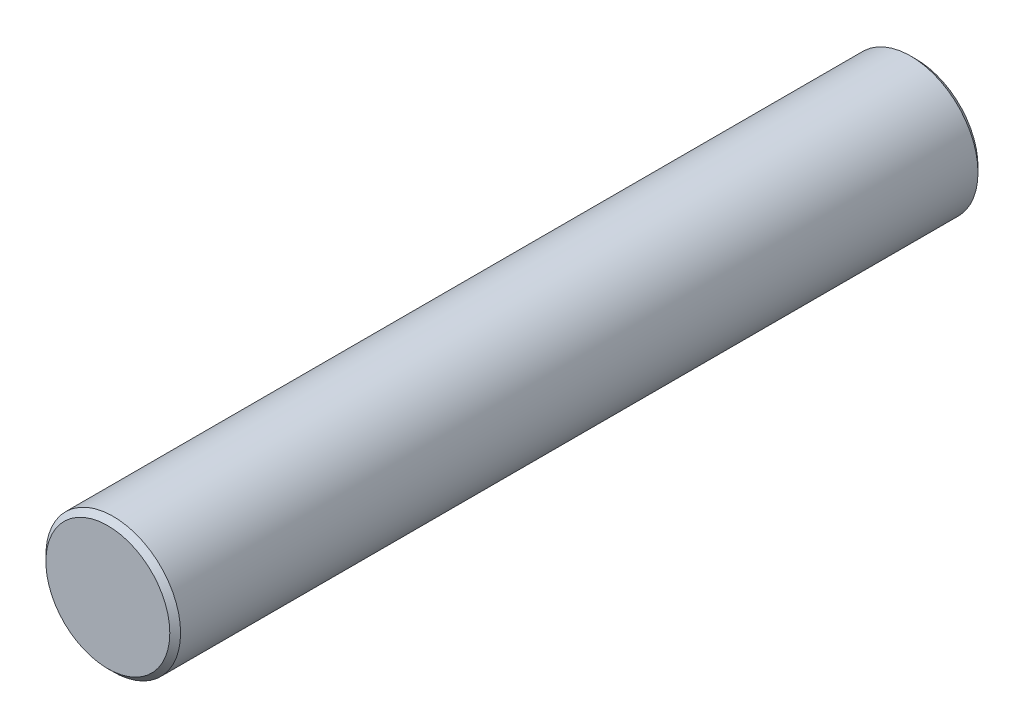
SolidWorks part; units mm, degrees
ref_plane "Front Plane" through (0, 0, 0) normal (0, 0, 1) x (1, 0, 0)
ref_plane "Top Plane" through (0, 0, 0) normal (0, 1, 0) x (1, 0, 0)
ref_plane "Right Plane" through (0, 0, 0) normal (1, 0, 0) x (0, 0, -1)
sketch "Sketch1" plane through (0, 0, 0) normal (0, 0, 1) x (1, 0, 0)
  circle A0 centre (0, 0) radius 2.5
  dimension "D1" = 5
extrude "Boss-Extrude1" add sketch "Sketch1" along normal blind 30
chamfer "Chamfer1" distance 0.2 angle 45 2 edges at (2.5, 0, 30) (2.5, 0, 0)
